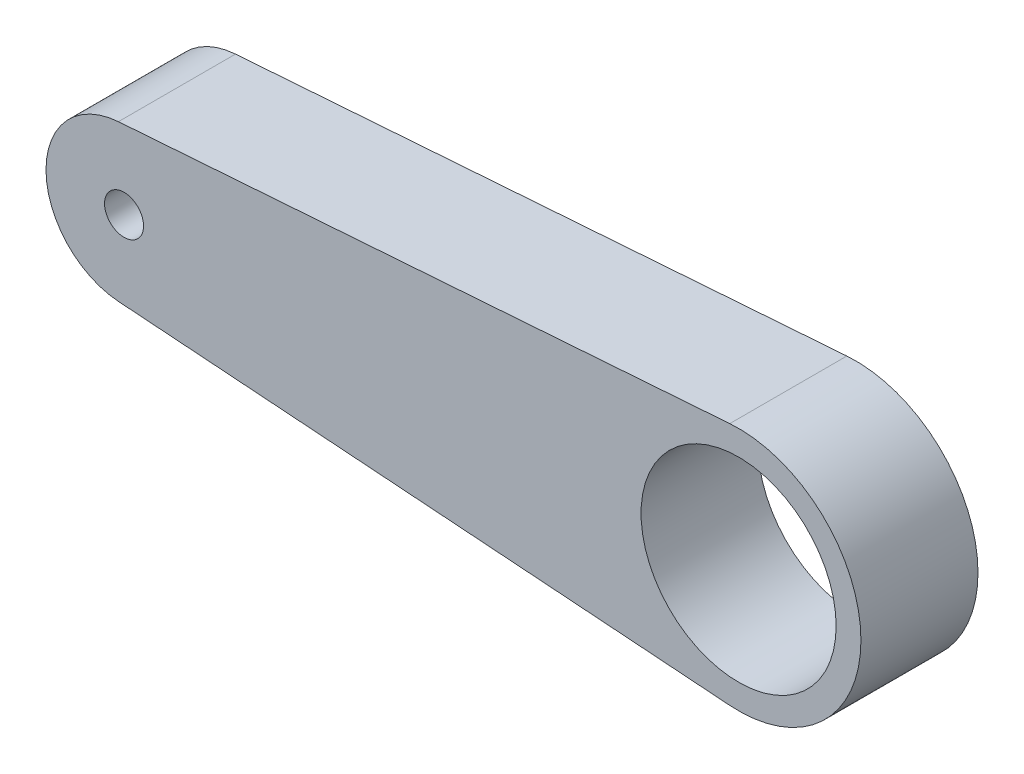
SolidWorks part; units mm, degrees
ref_plane "Alzado" through (0, 0, 0) normal (0, 0, 1) x (1, 0, 0)
ref_plane "Planta" through (0, 0, 0) normal (0, 1, 0) x (1, 0, 0)
ref_plane "Vista lateral" through (0, 0, 0) normal (1, 0, 0) x (0, 0, -1)
sketch "Croquis2" plane through (0, 0, 0) normal (0, 0, 1) x (1, 0, 0)
  line L0 (0, 0) -> (18.8856, 0) construction
  line L1 (-0.1442, 1.9948) -> (15.5239, 3.1274)
  line L4 (-0.1442, -1.9948) -> (15.5239, -3.1274)
  circle A0 centre (0, 0) radius 2
  circle A3 centre (0, 0) radius 0.5
  circle A4 centre (15.75, 0) radius 2.5
  circle A5 centre (15.75, 0) radius 3.1356
  dimension "D1" = 1
  dimension "D2" = 4
  dimension "D3" = 15.75
  dimension "D6" = 5
extrude "Saliente-Extruir1" add sketch "Croquis2" along normal mid plane 3
